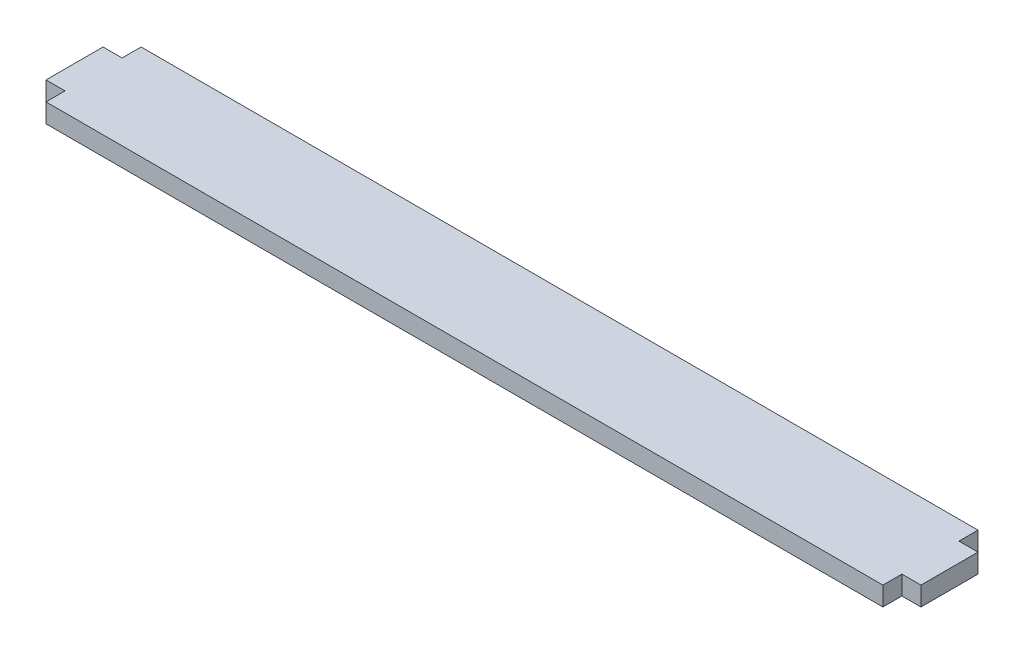
SolidWorks part; units mm, degrees
ref_plane "Front Plane" through (0, 0, 0) normal (0, 0, 1) x (1, 0, 0)
ref_plane "Top Plane" through (0, 0, 0) normal (0, 1, 0) x (1, 0, 0)
ref_plane "Right Plane" through (0, 0, 0) normal (1, 0, 0) x (0, 0, -1)
sketch "Sketch1" plane through (0, 0, 0) normal (0, 1, 0) x (1, 0, 0)
  line L0 (-69.85, -7.9375) -> (69.85, -7.9375)
  line L1 (69.85, -7.9375) -> (69.85, -4.7625)
  line L2 (69.85, -4.7625) -> (73.025, -4.7625)
  line L3 (73.025, -4.7625) -> (73.025, 4.7625)
  line L4 (73.025, 4.7625) -> (69.85, 4.7625)
  line L5 (69.85, 4.7625) -> (69.85, 7.9375)
  line L6 (69.85, 7.9375) -> (-69.85, 7.9375)
  line L7 (-69.85, 7.9375) -> (-69.85, 4.7625)
  line L8 (-69.85, 4.7625) -> (-73.025, 4.7625)
  line L9 (-73.025, 4.7625) -> (-73.025, -4.7625)
  line L10 (-73.025, -4.7625) -> (-69.85, -4.7625)
  line L11 (-69.85, -4.7625) -> (-69.85, -7.9375)
  point P9 (0, 7.9375)
  point P13 (73.025, 0)
  dimension "D1" = 3.175
  dimension "D2" = 9.525
  dimension "D3" = 15.875
  dimension "D4" = 139.7
extrude "Boss-Extrude1" add sketch "Sketch1" along normal blind 3.175
